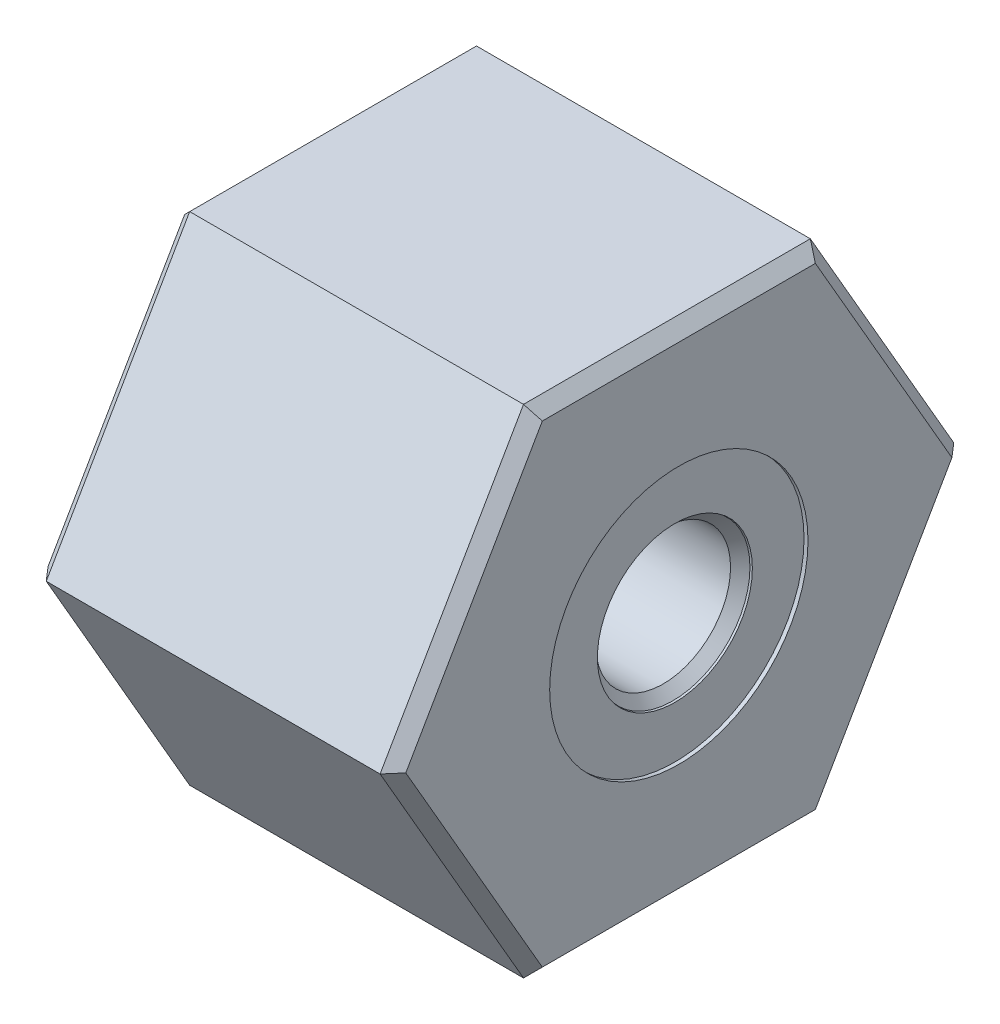
SolidWorks part; units mm, degrees
material "Alloy Steel"
ref_plane "Front Plane" through (0, 0, 0) normal (0, 0, 1) x (1, 0, 0)
ref_plane "Top Plane" through (0, 0, 0) normal (0, 1, 0) x (1, 0, 0)
ref_plane "Right Plane" through (0, 0, 0) normal (1, 0, 0) x (0, 0, -1)
sketch "Sketch1" plane through (0, 0, 0) normal (1, 0, 0) x (0, 0, -1)
  line L1 (9.1654, 15.875) -> (-9.1654, 15.875)
  line L2 (-9.1654, 15.875) -> (-18.3309, 0)
  line L3 (-18.3309, 0) -> (-9.1654, -15.875)
  line L4 (-9.1654, -15.875) -> (9.1654, -15.875)
  line L5 (9.1654, -15.875) -> (18.3309, 0)
  line L6 (18.3309, 0) -> (9.1654, 15.875)
  circle A0 centre (0, 0) radius 15.875 construction
  dimension "D1" = 31.75
extrude "Extrude1" add sketch "Sketch1" along normal blind 22.86
sketch "Sketch2" plane through (0, 0, 0) normal (0, 0, 1) x (1, 0, 0)
  line L0 (0, 12.2555) -> (0, 0)
  line L1 (0, 15.875) -> (0, 0) construction
  line L2 (22.86, 15.875) -> (22.86, 0) construction
  line L3 (22.86, 8.255) -> (22.606, 8.255)
  line L4 (22.606, 8.255) -> (22.606, 4.953)
  line L5 (22.606, 4.953) -> (22.479, 4.926)
  line L6 (22.479, 4.926) -> (21.8583, 4.3053)
  line L7 (14.478, 11.7221) -> (10.16, 11.7221)
  line L8 (10.16, 11.7221) -> (10.16, 12.2555)
  line L9 (14.478, 11.7221) -> (14.478, 5.0673)
  line L10 (10.16, 12.2555) -> (0, 12.2555)
  line L11 (0, 0) -> (34.3281, 0) construction
  line L12 (14.478, 5.0673) -> (15.24, 4.3053)
  line L13 (15.24, 4.3053) -> (21.8583, 4.3053)
  line L14 (22.86, 8.255) -> (22.86, 0)
  line L15 (0, 0) -> (22.86, 0)
  dimension "D1" = 24.511
  dimension "D2" = 10.16
  dimension "D3" = 23.4442
  dimension "D4" = 0.254
  dimension "D5" = 16.51
  dimension "D6" = 45
  dimension "D7" = 0.127
  dimension "D8" = 12
  dimension "D9" = 8.6106
  dimension "D10" = 45
  dimension "D11" = 10.1346
  dimension "D12" = 14.478
  dimension "D13" = 9.906
revolve "Cut-Revolve1" cut sketch "Sketch2" angle 360 about L11
chamfer "Chamfer1" distance 0.254 angle 45 1 edges at (0, 0, -12.2555)
chamfer "Chamfer3" distance 0.762 angle 45 6 edges at (0, 7.9375, 13.7482) (0, -7.9375, 13.7482) (0, 15.875, 0) (0, 7.9375, -13.7482) (0, -7.9375, -13.7482) (0, -15.875, 0)
chamfer "Chamfer4" distance 0.762 angle 45 6 edges at (22.86, 7.9375, 13.7482) (22.86, 15.875, 0) (22.86, -7.9375, 13.7482) (22.86, 7.9375, -13.7482) (22.86, -7.9375, -13.7482) (22.86, -15.875, 0)
fillet "Fillet1" radius 0.508 1 edges at (10.16, 0, -12.2555)
